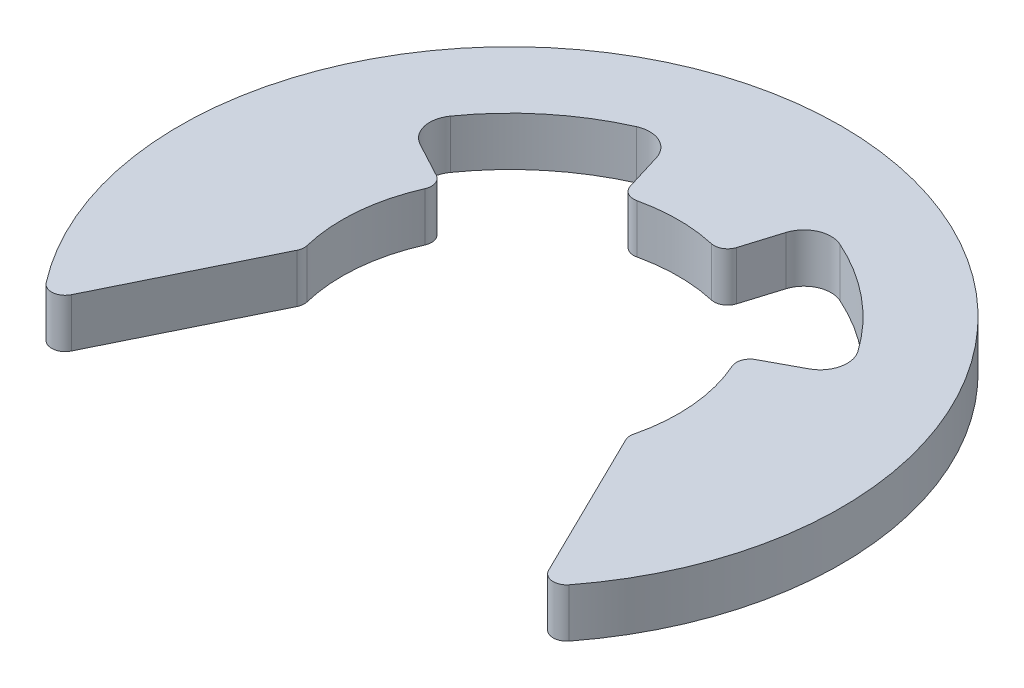
SolidWorks part; units mm, degrees
ref_plane "Front Plane" through (0, 0, 0) normal (0, 0, 1) x (1, 0, 0)
ref_plane "Top Plane" through (0, 0, 0) normal (0, 1, 0) x (1, 0, 0)
ref_plane "Right Plane" through (0, 0, 0) normal (1, 0, 0) x (0, 0, -1)
sketch "Sketch1" plane through (0, 0, 0) normal (0, 1, 0) x (1, 0, 0)
  circle A0 centre (0, 0) radius 6.1
  circle A1 centre (0, 0) radius 4.6
  circle A2 centre (0, 0) radius 3.1
  dimension "D1" = 12.2
  dimension "D2" = 1.5
  dimension "D3" = 3
sketch "Sketch2" plane through (0, 0, 0) normal (0, 1, 0) x (1, 0, 0)
  line L0 (-0.9804, 3.1936) -> (-1.1943, 3.8902)
  line L1 (1.1943, 3.8902) -> (0.9804, 3.1936)
  line L2 (2.9438, 1.5793) -> (3.586, 1.9238)
  line L3 (-2.9438, 1.5793) -> (-3.586, 1.9238)
  line L4 (3.0304, -0.9031) -> (4.4, -3.693)
  line L5 (-3.0304, -0.9031) -> (-4.4, -3.693)
  arc A0 (-3.586, 1.9238) -> (-3.7581, 2.6527) centre (-3.3496, 2.3644) cw
  arc A1 (3.586, 1.9238) -> (3.7581, 2.6527) centre (3.3496, 2.3644) ccw
  arc A2 (1.1943, 3.8902) -> (1.8762, 4.2) centre (1.6723, 3.7435) cw
  circle A3 centre (0, 0) radius 4.6 construction
  circle A4 centre (0, 0) radius 3.1 construction
  arc A5 (3.0119, -0.7338) -> (2.8335, 1.2576) centre (0, 0) ccw
  circle A6 centre (0, 0) radius 6.1 construction
  arc A7 (-2.8335, 1.2576) -> (-3.0119, -0.7338) centre (0, 0) ccw
  arc A8 (0.6861, 3.0231) -> (-0.6861, 3.0231) centre (0, 0) ccw
  arc A9 (3.7581, 2.6527) -> (1.8762, 4.2) centre (0, 0) ccw
  arc A10 (-1.8762, 4.2) -> (-3.7581, 2.6527) centre (0, 0) ccw
  arc A11 (4.8221, -3.736) -> (-4.8221, -3.736) centre (0, 0) ccw
  arc A12 (-1.1943, 3.8902) -> (-1.8762, 4.2) centre (-1.6723, 3.7435) ccw
  arc A13 (3.0304, -0.9031) -> (3.0119, -0.7338) centre (3.2548, -0.7929) cw
  arc A14 (2.9438, 1.5793) -> (2.8335, 1.2576) centre (3.062, 1.359) ccw
  arc A15 (-0.9804, 3.1936) -> (-0.6861, 3.0231) centre (-0.7414, 3.2669) ccw
  arc A16 (0.9804, 3.1936) -> (0.6861, 3.0231) centre (0.7414, 3.2669) cw
  arc A17 (-2.9438, 1.5793) -> (-2.8335, 1.2576) centre (-3.062, 1.359) cw
  arc A18 (-3.0304, -0.9031) -> (-3.0119, -0.7338) centre (-3.2548, -0.7929) ccw
  arc A19 (4.4, -3.693) -> (4.8221, -3.736) centre (4.6245, -3.5829) ccw
  arc A20 (-4.4, -3.693) -> (-4.8221, -3.736) centre (-4.6245, -3.5829) cw
  point P22 (-4.0535, 2.1746)
  point P23 (0, 6.1)
  point P26 (4.0535, 2.1746)
  point P29 (1.35, 4.3974)
  point P32 (-1.35, 4.3974)
  point P35 (2.9896, -0.82)
  point P38 (2.7317, 1.4655)
  point P41 (-0.9098, 2.9635)
  point P44 (0.9098, 2.9635)
  point P47 (-2.7317, 1.4655)
  point P50 (-2.9896, -0.82)
  point P53 (4.5704, -4.04)
  point P56 (-4.5704, -4.04)
  dimension "D7" = 0.5
  dimension "D8" = 0.25
  dimension "D9" = 0.25
  dimension "D1" = 1.8196
  dimension "D2" = 2.7
  dimension "D3" = 3.5
  dimension "D4" = 5.4634
  dimension "D5" = 2.3
  dimension "D6" = 10.14
extrude "Boss-Extrude2" add sketch "Sketch2" along normal blind 0.9
